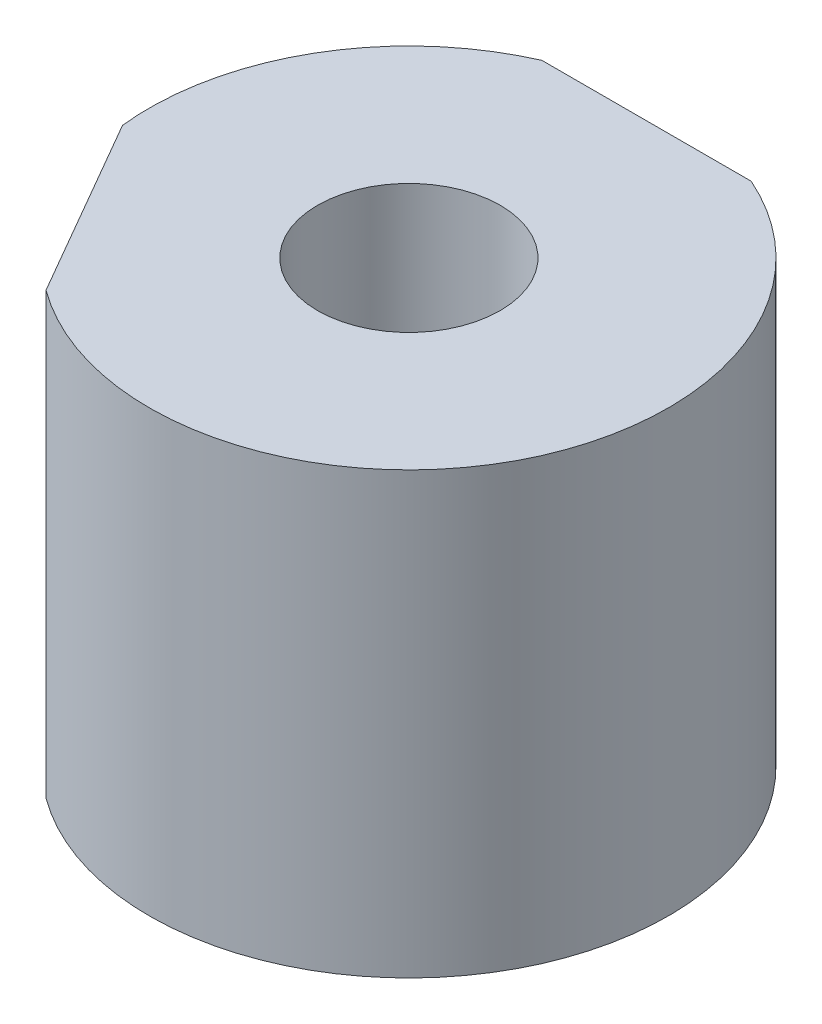
SolidWorks part; units mm, degrees
ref_plane "Front Plane" through (0, 0, 0) normal (0, 0, 1) x (1, 0, 0)
ref_plane "Top Plane" through (0, 0, 0) normal (0, 1, 0) x (1, 0, 0)
ref_plane "Right Plane" through (0, 0, 0) normal (1, 0, 0) x (0, 0, -1)
sketch "Sketch2" plane through (0, 0, 0) normal (0, 1, 0) x (1, 0, 0)
  line L0 (-5.9, 0) -> (5.9, 0) construction
  circle A0 centre (0, 0) radius 5.9
  dimension "D1" = 11.8
extrude "Boss-Extrude1" add sketch "Sketch2" along normal blind 10
sketch "Sketch3" plane through (0, 10, 0) normal (0, 1, 0) x (1, 0, 0)
  line L0 (-5.9, 0) -> (5.9, 0) construction
  circle A0 centre (0, 0) radius 5.9 construction
  circle A1 centre (0, 0) radius 2.075
  point P7 (0, 0)
  dimension "D1" = 4.15
extrude "Cut-Extrude1" cut sketch "Sketch3" against normal through all
sketch "Sketch4" plane through (0, 10, 0) normal (0, 1, 0) x (1, 0, 0)
  line L0 (0, 0) -> (0, 5.9) construction
  line L2 (-5.9, 6.4) -> (5.9, 6.4)
  line L3 (-5.9, 6.4) -> (-5.9, 5.4)
  line L4 (-5.9, 5.4) -> (5.9, 5.4)
  line L5 (5.9, 6.4) -> (5.9, 5.4)
  line L6 (0, 5.4) -> (0, 6.4) construction
  line L7 (-5.9, 5.9) -> (5.9, 5.9) construction
  circle A0 centre (0, 0) radius 5.9 construction
  dimension "D1" = 0.5
extrude "Cut-Extrude2" cut sketch "Sketch4" against normal through all
pattern_circular "CirPattern1" count 2 every 120 about axis through (0, 10, 0) along (0, 1, 0) of "Cut-Extrude2"
